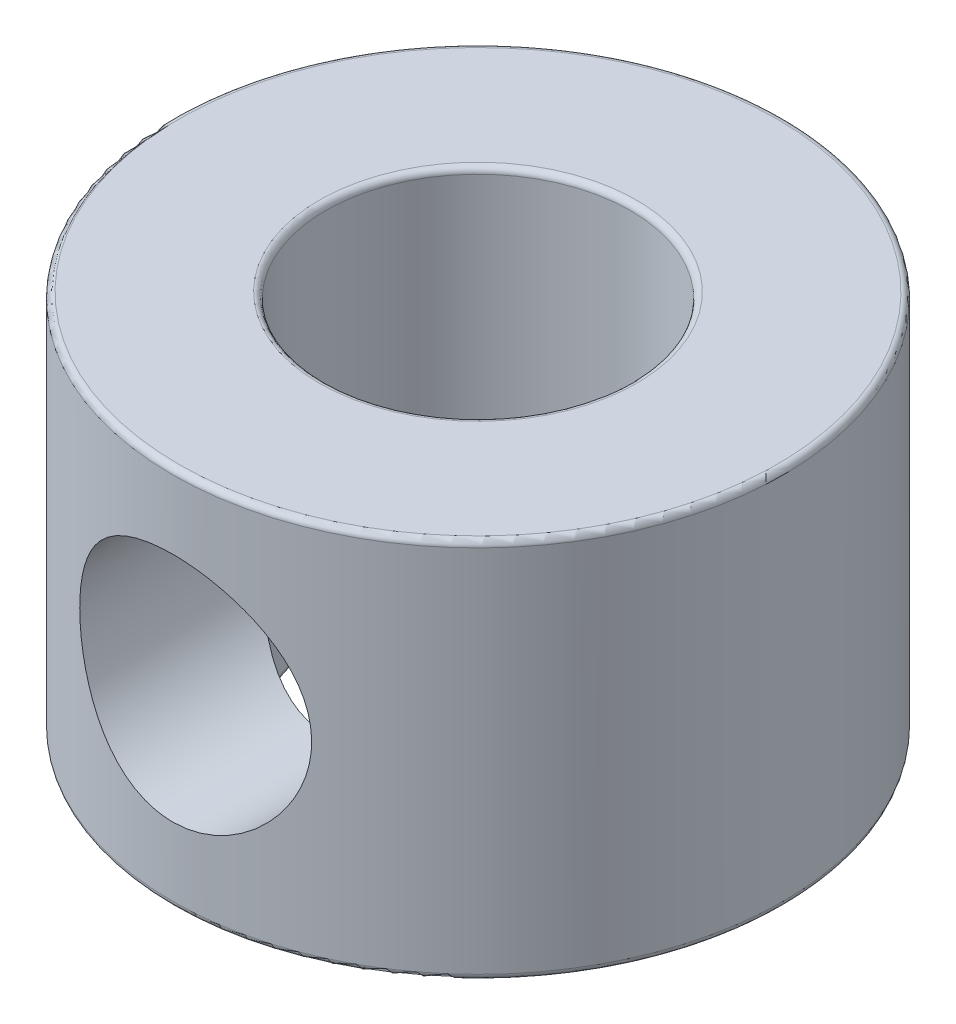
SolidWorks part; units mm, degrees
ref_plane "前视基准面" through (0, 0, 0) normal (0, 0, 1) x (1, 0, 0)
ref_plane "上视基准面" through (0, 0, 0) normal (0, 1, 0) x (1, 0, 0)
ref_plane "右视基准面" through (0, 0, 0) normal (1, 0, 0) x (0, 0, -1)
ref_plane "基准面4" through (0, 0, 0) normal (0, 0, -1) x (-1, 0, 0)
sketch "草图1" plane through (0, 0, 0) normal (0, 0, -1) x (-1, 0, 0)
  line L0 (-6.35, -3.9688) -> (0, -3.9688)
  line L1 (0, -3.9688) -> (0, 3.9688)
  line L2 (0, 3.9688) -> (-6.35, 3.9688)
  line L3 (-6.35, 3.9688) -> (-6.35, -3.9688)
  line L4 (0, -3.9688) -> (0, 3.9688) construction
revolve "旋转1" add sketch "草图1" angle 360 about L4
hole_wizard "孔1" positions "草图3" profile "草图2" legacy
sketch "草图3" plane through (0, -3.9688, 0) normal (0, -1, 0) x (-1, 0, 0)
  point P0 (0, 0)
sketch "草图2" plane through (0, -3.9688, 0) normal (1, 0, 0) x (0, 0, -1)
  line L0 (0, 0) -> (0, 7.9375)
  line L1 (0, 7.9375) -> (3.175, 7.9375)
  line L2 (3.175, 7.9375) -> (3.175, 0)
  line L3 (3.175, 0) -> (0, 0)
  line L4 (0, 110) -> (0, -10) construction
  dimension "直径" = 6.35
  dimension "深度" = 7.9375
ref_plane "基准面5" through (0, 0, 2.0635) normal (0, 0, -1) x (-1, 0, 0)
hole_wizard "孔2" positions "草图5" profile "草图4" legacy
sketch "草图5" plane through (0, 0, 2.0635) normal (0, 0, -1) x (-1, 0, 0)
  point P0 (0, 0)
sketch "草图4" plane through (0, 0, 2.0635) normal (1, 0, 0) x (0, 1, 0)
  line L0 (0, 0) -> (0, 4.2865)
  line L1 (0, 4.2865) -> (2.413, 4.2865)
  line L2 (2.413, 4.2865) -> (2.413, 0)
  line L3 (2.413, 0) -> (0, 0)
  line L4 (0, 110) -> (0, -10) construction
  dimension "直径" = 4.826
  dimension "深度" = 4.2865
fillet "圆角1" radius 0.127 4 edges at (0, -3.9688, 6.35) (0, 3.9688, 6.35) (0, 3.9688, -3.175) (0, -3.9688, -3.175)
